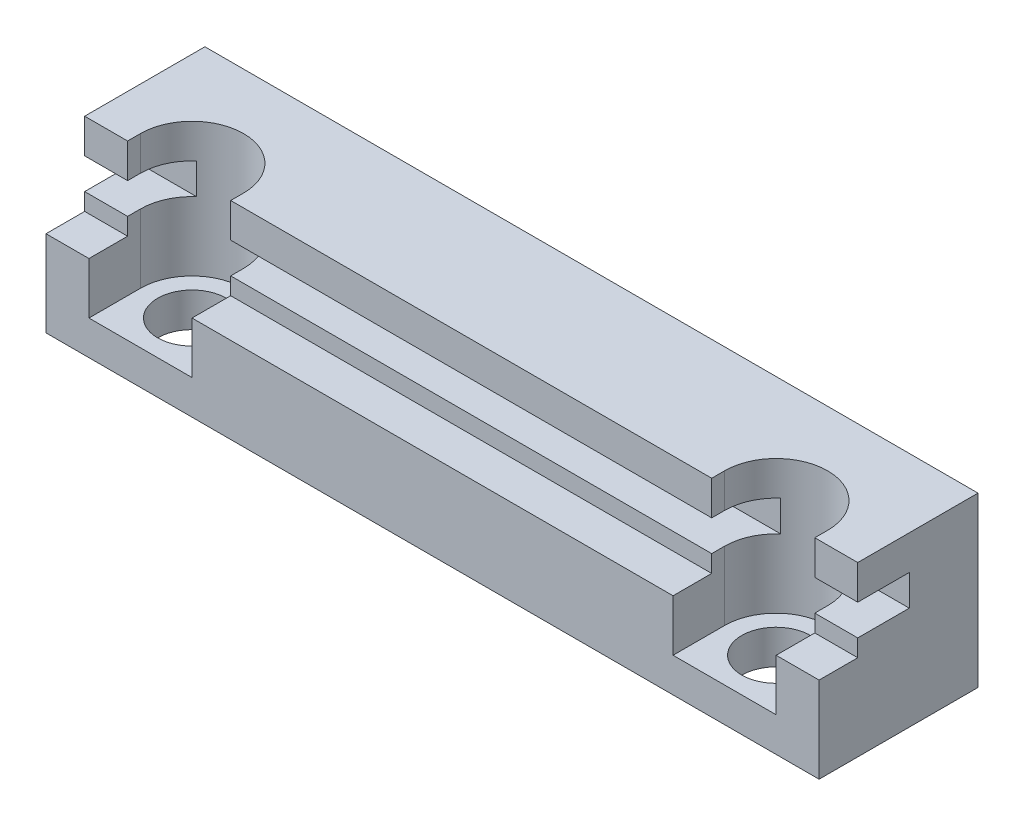
SolidWorks part; units mm, degrees
ref_plane "Спереди" through (0, 0, 0) normal (0, 0, 1) x (1, 0, 0)
ref_plane "Сверху" through (0, 0, 0) normal (0, 1, 0) x (1, 0, 0)
ref_plane "Справа" through (0, 0, 0) normal (1, 0, 0) x (0, 0, -1)
sketch "Эскиз1" plane through (0, 0, 0) normal (1, 0, 0) x (0, 0, -1)
  line L0 (0, 5) -> (0, 6)
  line L1 (0, 6) -> (3, 6)
  line L2 (3, 6) -> (3, 7.8)
  line L3 (3, 7.8) -> (0, 7.8)
  line L4 (0, 7.8) -> (0, 9.8)
  line L5 (0, 9.8) -> (7, 9.8)
  line L6 (7, 9.8) -> (7, 0)
  line L7 (7, 0) -> (0, 0)
  line L8 (-18.75, 9.8) -> (-18.75, 0) construction
  line L9 (-18.75, 0) -> (0, 0) construction
  line L10 (-18.75, 9.8) -> (0, 9.8) construction
  line L11 (0.75, 6) -> (0.75, 0) construction
  line L13 (-2.25, 5) -> (-2.25, 0)
  line L14 (-2.25, 0) -> (0, 0)
  line L15 (-2.25, 5) -> (0, 5)
  dimension "D1" = 43.5
  dimension "D2" = 1.8
  dimension "D3" = 2
  dimension "D4" = 3
  dimension "D5" = 6
  dimension "D6" = 7
  dimension "D7" = 19.5
  dimension "D8" = 3
  dimension "D9" = 1
extrude "Бобышка-Вытянуть1" add sketch "Эскиз1" along normal blind 45
sketch "Эскиз2" plane through (0, 9.8, 0) normal (0, 1, 0) x (1, 0, 0)
  line L0 (5.5, 0.75) -> (39.5, 0.75) construction
  line L1 (45, -2.25) -> (0, -2.25) construction
  line L2 (22.5, 7) -> (22.5, 0.75) construction
  line L3 (45, 7) -> (0, 7) construction
  circle A0 centre (5.5, 0.75) radius 2
  circle A1 centre (39.5, 0.75) radius 2
  dimension "D1" = 3
  dimension "D3" = 4
  dimension "D4" = 4
  dimension "D2" = 34
extrude "Вырез-Вытянуть1" cut sketch "Эскиз2" against normal through all
sketch "Эскиз3" plane through (0, 9.8, 0) normal (0, 1, 0) x (1, 0, 0)
  line L0 (2.5, 0.75) -> (2.5, -2.25)
  line L1 (45, -2.25) -> (0, -2.25) construction
  line L2 (2.5, -2.25) -> (8.5, -2.25)
  line L3 (8.5, -2.25) -> (8.5, 0.75)
  line L4 (36.5, 0.75) -> (36.5, -2.25)
  line L5 (36.5, -2.25) -> (42.5, -2.25)
  line L6 (42.5, -2.25) -> (42.5, 0.75)
  arc A0 (8.5, 0.75) -> (2.5, 0.75) centre (5.5, 0.75) ccw
  arc A1 (42.5, 0.75) -> (36.5, 0.75) centre (39.5, 0.75) ccw
  dimension "D1" = 6
extrude "Вырез-Вытянуть2" cut sketch "Эскиз3" against normal blind 7.8
